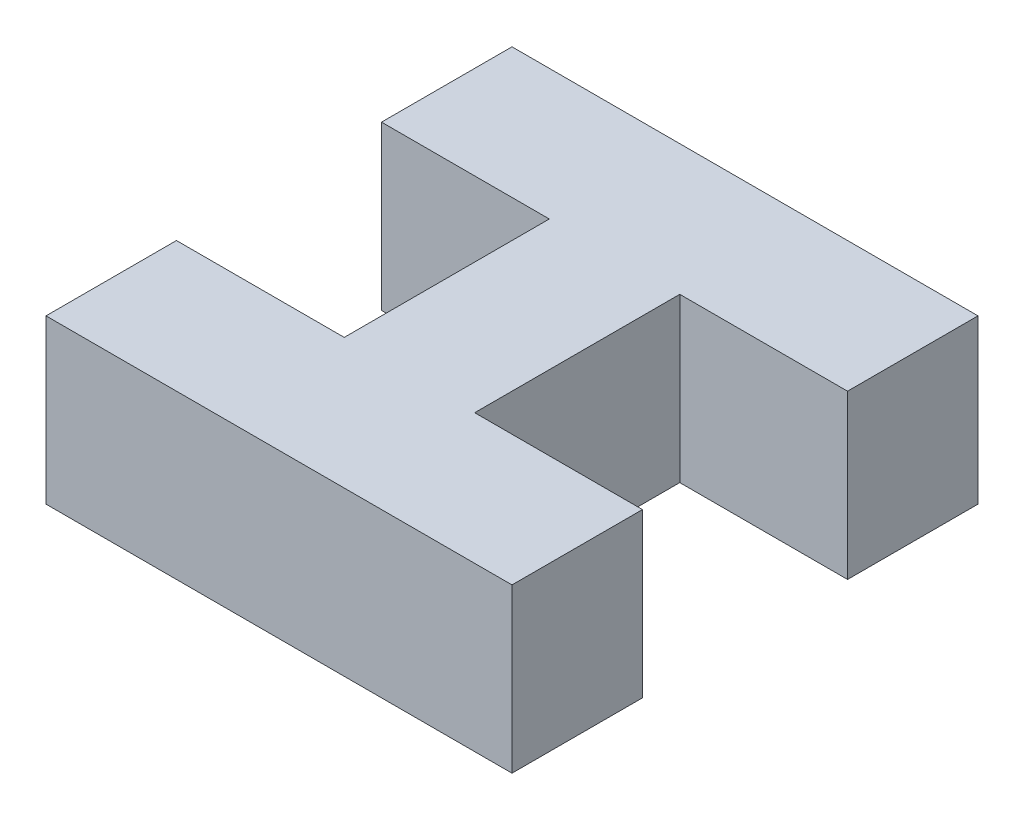
SolidWorks part; units mm, degrees
ref_plane "Front Plane" through (0, 0, 0) normal (0, 0, 1) x (1, 0, 0)
ref_plane "Top Plane" through (0, 0, 0) normal (0, 1, 0) x (1, 0, 0)
ref_plane "Right Plane" through (0, 0, 0) normal (1, 0, 0) x (0, 0, -1)
sketch "Sketch2" plane through (0, 0, 0) normal (0, 1, 0) x (1, 0, 0)
  line L0 (-3.1437, 3.1438) -> (-7.1438, 3.1437)
  line L1 (-7.1438, -7.1437) -> (7.1437, -7.1437)
  line L2 (-7.1438, -7.1437) -> (-7.1438, -3.1437)
  line L3 (-7.1438, 7.1437) -> (7.1437, 7.1437)
  line L4 (7.1437, -7.1437) -> (7.1437, -3.1437)
  line L5 (3.1437, 3.1438) -> (7.1437, 3.1437)
  line L6 (-3.1437, -3.1438) -> (-7.1438, -3.1437)
  line L7 (-3.1437, -3.1438) -> (-2, -3.1438)
  line L9 (-3.1437, 3.1438) -> (-2, 3.1438)
  line L11 (-2, 2) -> (-2, 3.1438)
  line L12 (2, 2) -> (2, 3.1438)
  line L14 (-2, -2) -> (-2, 2)
  line L16 (2, -2) -> (2, 2)
  line L19 (3.1437, -3.1438) -> (7.1437, -3.1437)
  line L20 (-2, -2) -> (-2, -3.1438)
  line L21 (2, -2) -> (2, -3.1438)
  line L22 (-7.1438, 3.1437) -> (-7.1438, 7.1437)
  line L23 (7.1437, 3.1437) -> (7.1437, 7.1437)
  line L24 (2, 3.1438) -> (3.1437, 3.1438)
  line L25 (2, -3.1438) -> (3.1437, -3.1438)
  point P0 (0, 0)
  point P6 (0, 0)
  point P11 (0, 0)
  dimension "D1" = 14.2875
  dimension "D2" = 14.2875
  dimension "D3" = 4
  dimension "D4" = 4
extrude "Boss-Extrude1" add sketch "Sketch2" along normal blind 5
